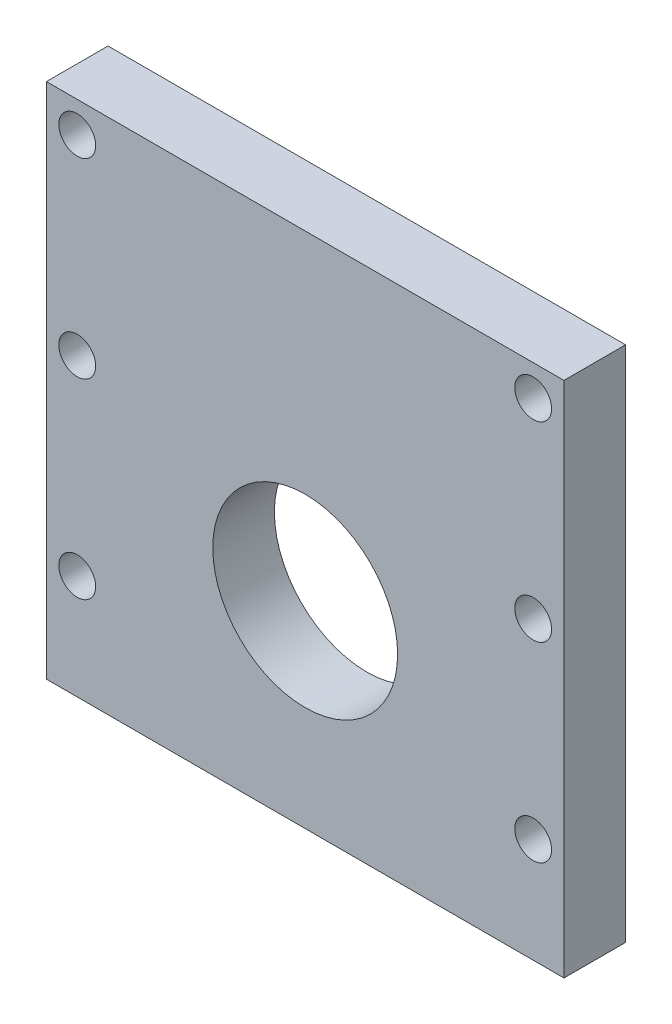
SolidWorks part; units mm, degrees
material "6061-T6 (SS)"
ref_plane "Front Plane" through (0, 0, 0) normal (0, 0, 1) x (1, 0, 0)
ref_plane "Top Plane" through (0, 0, 0) normal (0, 1, 0) x (1, 0, 0)
ref_plane "Right Plane" through (0, 0, 0) normal (1, 0, 0) x (0, 0, -1)
sketch "Sketch1" plane through (0, 0, 0) normal (0, 0, 1) x (1, 0, 0)
  line L1 (0, 0) -> (53.34, 0)
  line L2 (0, 0) -> (0, 53.34)
  line L3 (0, 53.34) -> (53.34, 53.34)
  line L4 (53.34, 0) -> (53.34, 53.34)
  dimension "D1" = 53.34
  dimension "D2" = 53.34
extrude "Boss-Extrude1" add sketch "Sketch1" along normal blind 6.35
sketch "Sketch2" plane through (0, 0, 6.35) normal (0, 0, 1) x (1, 0, 0)
  line L0 (53.34, 53.34) -> (0, 53.34) construction
  circle A0 centre (26.67, 20.32) radius 9.525
  point P4 (26.67, 53.34)
  dimension "D1" = 19.05
  dimension "D3" = 33.02
  dimension "D2" = 0
extrude "Cut-Extrude1" cut sketch "Sketch2" against normal through all both and the other way through all
hole_wizard "#6 Clearance Hole1" positions "Sketch3" profile "Sketch4" hole size "#6" standard "ANSI Inch" end condition up to next
sketch "Sketch3" plane through (0, 0, 6.35) normal (0, 0, 1) x (1, 0, 0)
  line L0 (0, 53.34) -> (0, 0) construction
  line L2 (53.34, 53.34) -> (0, 53.34) construction
  line L3 (53.34, 0) -> (53.34, 53.34) construction
  point P0 (3.175, 50.165)
  point P24 (50.165, 50.165)
  point P25 (50.165, 10.795)
  point P26 (3.175, 10.795)
  point P32 (3.175, 30.48)
  point P34 (50.165, 30.48)
  dimension "D1" = 3.175
  dimension "D2" = 3.175
  dimension "D3" = 2
  dimension "D5" = 3.175
  dimension "D6" = 39.37
  dimension "D7" = 3.175
  dimension "D8" = 3.175
  dimension "D9" = 19.685
  dimension "D10" = 19.685
  dimension "D11" = 3.175
  dimension "D4" = 2
sketch "Sketch4" plane through (3.175, 50.165, 6.35) normal (1, 0, 0) x (0, -1, 0)
  line L0 (0, 0) -> (0, 6.35)
  line L1 (0, 6.35) -> (1.8986, 6.35)
  line L2 (1.8986, 6.35) -> (1.8986, 0)
  line L5 (1.8986, 0) -> (0, 0)
  line L11 (0, -6.35) -> (0, 107.95) construction
  dimension "Thru Hole Dia." = 3.7973
  dimension "Thru Hole Depth" = 6.35
